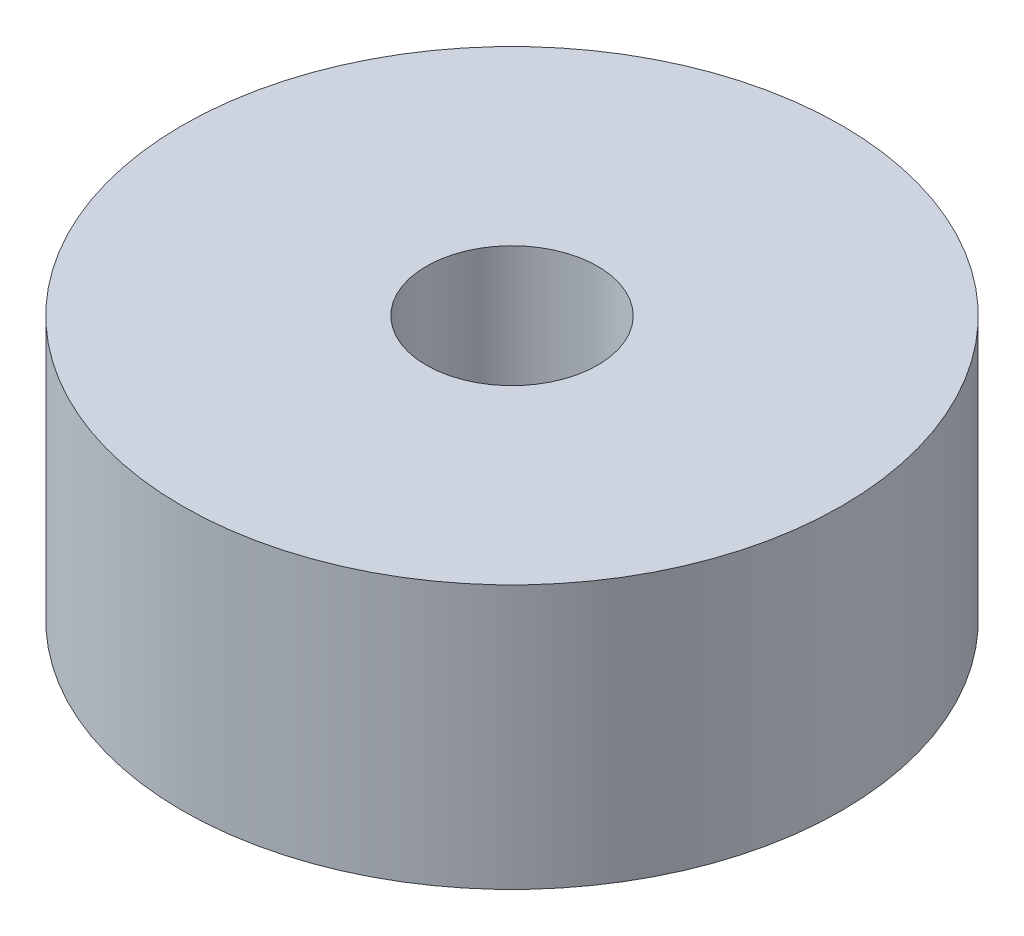
SolidWorks part; units mm, degrees
ref_plane "Front Plane" through (0, 0, 0) normal (0, 0, 1) x (1, 0, 0)
ref_plane "Top Plane" through (0, 0, 0) normal (0, 1, 0) x (1, 0, 0)
ref_plane "Right Plane" through (0, 0, 0) normal (1, 0, 0) x (0, 0, -1)
sketch "Sketch1" plane through (0, 0, 0) normal (0, 1, 0) x (1, 0, 0)
  circle A0 centre (0, 0) radius 12.5
  dimension "D1" = 25
extrude "Boss-Extrude1" add sketch "Sketch1" along normal blind 10
sketch "Sketch3" plane through (0, 10, 0) normal (0, 1, 0) x (1, 0, 0)
  circle A0 centre (0, 0) radius 3.25
  dimension "D1" = 6.5
extrude "Cut-Extrude2" cut sketch "Sketch3" against normal through all contours A0
